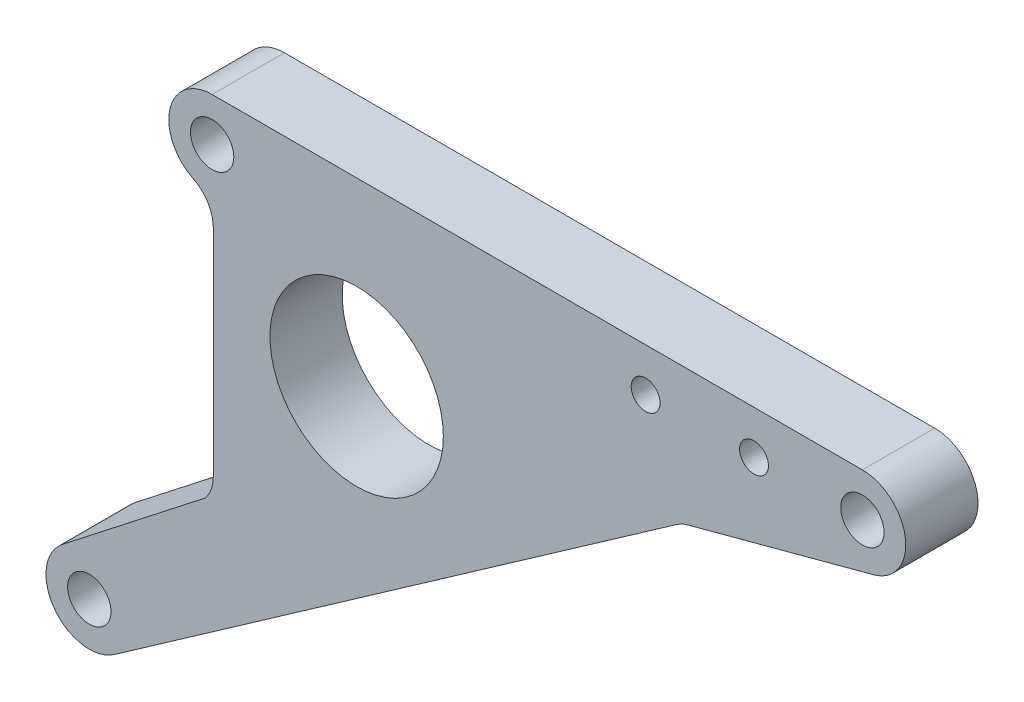
SolidWorks part; units mm, degrees
ref_plane "Front Plane" through (0, 0, 0) normal (0, 0, 1) x (1, 0, 0)
ref_plane "Top Plane" through (0, 0, 0) normal (0, 1, 0) x (1, 0, 0)
ref_plane "Right Plane" through (0, 0, 0) normal (1, 0, 0) x (0, 0, -1)
sketch "Sketch2" plane through (0, 0, 0) normal (0, 0, 1) x (1, 0, 0)
  line L0 (16.0863, 54.5463) -> (-73.9137, 54.5463)
  line L1 (-73.7548, 38.6689) -> (-73.7548, 8.8334)
  line L2 (-74.8496, 5.711) -> (-94.6077, -9.7256)
  line L3 (-87.4722, -19.3686) -> (-9.6423, 35.1285)
  line L4 (-8.0685, 35.8624) -> (17.6392, 42.7507)
  line L5 (-90.9137, -14.4537) -> (-33.4004, -14.4537) construction
  arc A0 (-73.9137, 54.5463) -> (-76.5543, 43.1586) centre (-73.9137, 48.5463) ccw
  arc A1 (-76.5543, 43.1586) -> (-73.7548, 38.6689) centre (-78.7548, 38.6689) cw
  arc A2 (-73.7548, 8.8334) -> (-74.8496, 5.711) centre (-78.7548, 8.8334) cw
  arc A3 (-94.6077, -9.7256) -> (-87.4722, -19.3686) centre (-90.9137, -14.4537) ccw
  arc A4 (17.6392, 42.7507) -> (16.0863, 54.5463) centre (16.0863, 48.5463) ccw
  circle A5 centre (16.0863, 48.5463) radius 3
  circle A6 centre (1.0863, 48.5463) radius 2
  circle A7 centre (-13.9137, 48.5463) radius 2
  circle A8 centre (-73.9137, 48.5463) radius 3
  circle A9 centre (-90.9137, -14.4537) radius 3
  circle A10 centre (-53.9137, 29.5463) radius 12
  arc A11 (-8.0685, 35.8624) -> (-9.6423, 35.1285) centre (-6.7744, 31.0327) ccw
  point P24 (-79.7586, 49.9016)
  point P25 (0, 0)
  point P29 (0, 0)
  dimension "D5" = 6
  dimension "D6" = 24
  dimension "D7" = 4
  dimension "D8" = 4
  dimension "D9" = 6
  dimension "D10" = 6
  dimension "D15" = 6
  dimension "D16" = 6
  dimension "D17" = 5
  dimension "D18" = 5
  dimension "D22" = 5
  dimension "D1" = 107
  dimension "D2" = 92
  dimension "D3" = 77
  dimension "D4" = 17
  dimension "D11" = 6
  dimension "D12" = 25
  dimension "D13" = 38
  dimension "D14" = 35
  dimension "D19" = 15
  dimension "D20" = 37
  dimension "D21" = 69
extrude "Boss-Extrude1" add sketch "Sketch2" along normal blind 10
